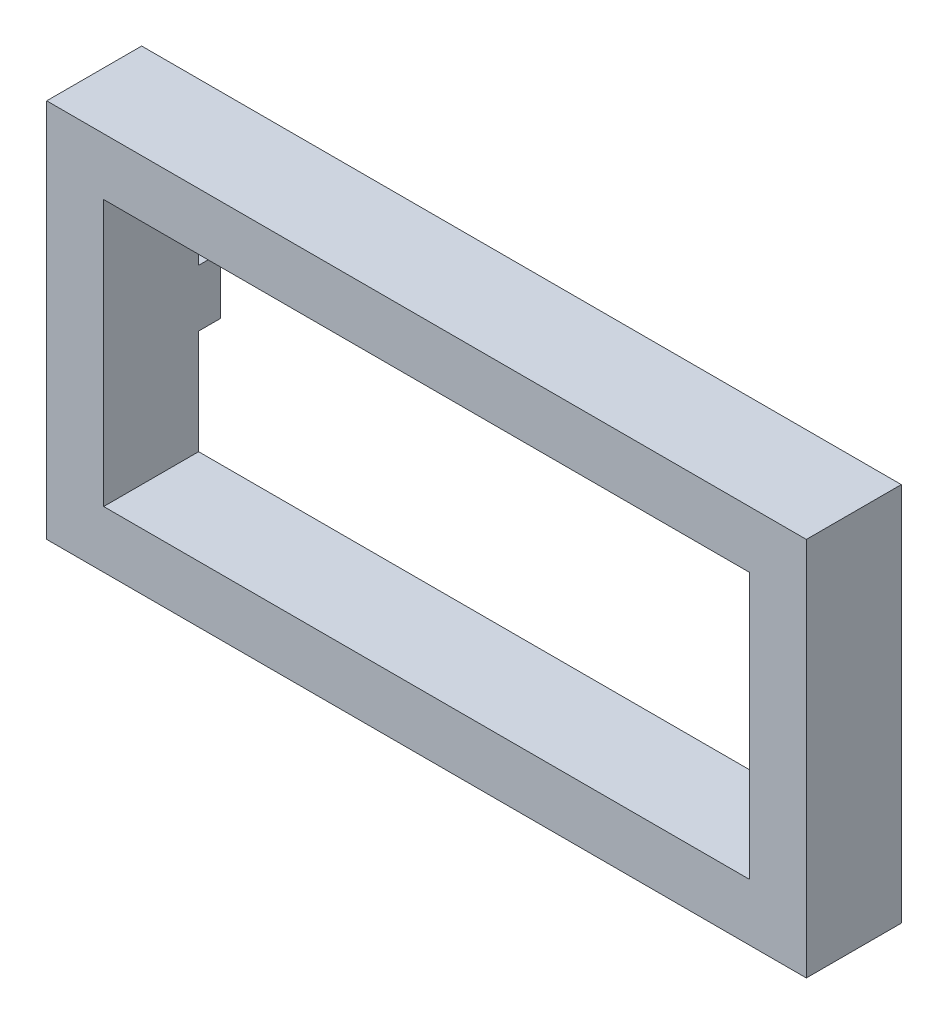
SolidWorks part; units mm, degrees
ref_plane "Front Plane" through (0, 0, 0) normal (0, 0, 1) x (1, 0, 0)
ref_plane "Top Plane" through (0, 0, 0) normal (0, 1, 0) x (1, 0, 0)
ref_plane "Right Plane" through (0, 0, 0) normal (1, 0, 0) x (0, 0, -1)
sketch "Sketch1" plane through (0, 0, 0) normal (0, 0, 1) x (1, 0, 0)
  line L1 (205.4167, -100) -> (-194.5833, -100)
  line L2 (205.4167, -100) -> (205.4167, 100)
  line L3 (205.4167, 100) -> (-194.5833, 100)
  line L4 (-194.5833, -100) -> (-194.5833, 100)
  line L7 (175.4167, -70) -> (-164.5833, -70)
  line L8 (175.4167, -70) -> (175.4167, 70)
  line L9 (175.4167, 70) -> (-164.5833, 70)
  line L10 (-164.5833, -70) -> (-164.5833, 70)
  point P0 (0, 0)
  point P6 (0, 0)
  dimension "D1" = 200
  dimension "D2" = 400
  dimension "D3" = 30
  dimension "D4" = 30
  dimension "D5" = 30
  dimension "D6" = 30
extrude "Boss-Extrude1" add sketch "Sketch1" along normal blind 50
sketch "Sketch2" plane through (0, 0, 0) normal (0, 0, -1) x (-1, 0, 0)
  line L0 (-205.4167, 100) -> (194.5833, 100) construction
  line L1 (-70.4167, 92.5) -> (-85.4167, 92.5)
  line L2 (-70.4167, 92.5) -> (-70.4167, 77.5)
  line L3 (-70.4167, 77.5) -> (-85.4167, 77.5)
  line L4 (-85.4167, 92.5) -> (-85.4167, 77.5)
  line L5 (-70.4167, -77.5) -> (-85.4167, -77.5)
  line L6 (-70.4167, -77.5) -> (-70.4167, -92.5)
  line L7 (-70.4167, -92.5) -> (-85.4167, -92.5)
  line L8 (-85.4167, -77.5) -> (-85.4167, -92.5)
  line L10 (-205.4167, -100) -> (-205.4167, 100) construction
  line L11 (194.5833, -100) -> (-205.4167, -100) construction
  line L22 (-197.9167, 7.4934) -> (-197.9167, -7.5066)
  line L23 (-182.9167, 7.5023) -> (-197.9167, 7.4934)
  line L24 (-182.9167, -7.4977) -> (-197.9167, -7.5066)
  line L25 (-182.9167, 7.5023) -> (-182.9167, -7.4977)
  dimension "D1" = 15
  dimension "D2" = 7.5
  dimension "D3" = 120
  dimension "D4" = 7.5
extrude "Cut-Extrude1" cut sketch "Sketch2" against normal blind 40
sketch "Sketch3" plane through (0, 0, 0) normal (0, 0, -1) x (-1, 0, 0)
  line L0 (164.5833, 70) -> (164.5833, -70) construction
  line L1 (169.5833, 10) -> (189.5833, 10)
  line L2 (169.5833, 10) -> (169.5833, -10)
  line L3 (169.5833, -10) -> (189.5833, -10)
  line L4 (189.5833, 10) -> (189.5833, -10)
  line L10 (164.5833, 15) -> (194.5833, 15)
  line L11 (164.5833, 15) -> (164.5833, -15)
  line L12 (164.5833, -15) -> (194.5833, -15)
  line L13 (194.5833, 15) -> (194.5833, -15)
  point P0 (179.9332, 0)
  point P14 (179.9332, 0)
  dimension "D1" = 30
  dimension "D2" = 30
  dimension "D3" = 5
  dimension "D4" = 20
  dimension "D5" = 20
  dimension "D6" = 5
extrude "Boss-Extrude2" add sketch "Sketch3" along normal blind 11.5
sketch "Sketch4" plane through (205.4167, 0, 0) normal (1, 0, 0) x (0, 0, -1)
  line L0 (-50, -100) -> (-50, 100) construction
  point P0 (-50, 0)
